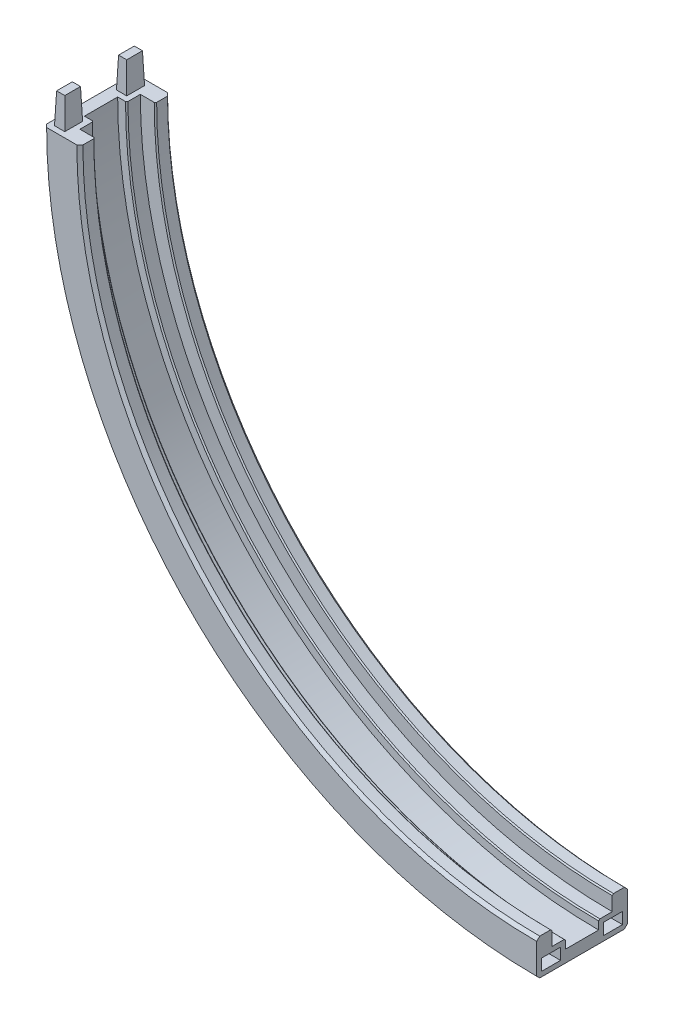
SolidWorks part; units mm, degrees
ref_plane "Plan de face" through (0, 0, 0) normal (0, 0, 1) x (1, 0, 0)
ref_plane "Plan de dessus" through (0, 0, 0) normal (0, 1, 0) x (1, 0, 0)
ref_plane "Plan de droite" through (0, 0, 0) normal (1, 0, 0) x (0, 0, -1)
sketch "Esquisse1" plane through (0, 0, 0) normal (0, 0, 1) x (1, 0, 0)
  line L0 (-159.1549, 159.1549) -> (0, 159.1549) construction
  line L1 (0, 159.1549) -> (0, 0) construction
  circle A0 centre (0, 159.1549) radius 159.1549 construction
  arc A1 (0, 0) -> (-159.1549, 159.1549) centre (0, 159.1549) cw
  dimension "D1" = 318.3099
  dimension "D2" = 90
sketch "Esquisse2" plane through (0, 0, 0) normal (1, 0, 0) x (0, 0, -1)
  line L0 (-5.5, 0) -> (5.5, 0)
  line L2 (-10, 8) -> (-15, 8)
  line L5 (-15, 8) -> (-15, -4)
  line L6 (-15, -4) -> (15, -4)
  line L7 (15, -4) -> (15, 8)
  line L10 (15, 8) -> (10, 8)
  line L18 (-10, 8) -> (-10, 3)
  line L19 (10, 8) -> (10, 3)
  line L20 (-10, 3) -> (-5.5, 3)
  line L21 (-5.5, 3) -> (-5.5, 0)
  line L22 (10, 3) -> (5.5, 3)
  line L23 (5.5, 3) -> (5.5, 0)
  point P4 (0, 0)
  point P17 (0, -4)
  dimension "D1" = 4
  dimension "D2" = 20
  dimension "D3" = 5
  dimension "D4" = 5
  dimension "D5" = 3
  dimension "D6" = 11
sweep "Balayage1" add profiles "Esquisse2" path "Esquisse1"
chamfer "Chanfrein1" distance 1 angle 45 4 edges at (-115.368, 43.787, -15) (-115.368, 43.787, 15) (-106.8827, 52.2723, -15) (-106.8827, 52.2723, 15)
chamfer "Chanfrein3" distance 0.4 angle 45 4 edges at (-110.4182, 48.7367, 5.5) (-106.8827, 52.2723, 10) (-106.8827, 52.2723, -10) (-110.4182, 48.7367, -5.5)
sketch "Esquisse5" plane through (0, 0, 0) normal (1, 0, 0) x (0, 0, -1)
  line L0 (-15, 7) -> (-15, -3) construction
  line L1 (-13.4, -2.4) -> (-7.1, -2.4)
  line L2 (-13.4, -2.4) -> (-13.4, 1.4)
  line L3 (-13.4, 1.4) -> (-7.1, 1.4)
  line L4 (-7.1, -2.4) -> (-7.1, 1.4)
  line L5 (-13.4, -2.4) -> (-7.1, 1.4) construction
  line L6 (-13.4, 1.4) -> (-7.1, -2.4) construction
  line L7 (-14, -4) -> (14, -4) construction
  line L8 (-5.9, 3) -> (-10, 3) construction
  line L9 (-5.5, 0) -> (-5.5, 2.6) construction
  line L10 (0, 89.7352) -> (0, -89.7352) construction
  line L11 (13.4, -2.4) -> (7.1, -2.4)
  line L12 (7.1, -2.4) -> (7.1, 1.4)
  line L13 (13.4, 1.4) -> (7.1, 1.4)
  line L14 (13.4, -2.4) -> (13.4, 1.4)
  point P0 (-10.25, -0.5)
  dimension "D1" = 1.6
  dimension "D2" = 1.6
  dimension "D3" = 1.6
  dimension "D4" = 1.6
extrude "Enlèv. mat.-Extru.1" cut sketch "Esquisse5" against normal blind 11 draft 2
sketch "Esquisse6" plane through (0, 159.1549, 0) normal (0, 1, 0) x (1, 0, 0)
  line L0 (-152.1549, -15) -> (-162.1549, -15) construction
  line L1 (-157.9549, -13.2) -> (-161.3549, -13.2)
  line L2 (-157.9549, -13.2) -> (-157.9549, -7.3)
  line L3 (-157.9549, -7.3) -> (-161.3549, -7.3)
  line L4 (-161.3549, -13.2) -> (-161.3549, -7.3)
  line L5 (-157.9549, -13.2) -> (-161.3549, -7.3) construction
  line L6 (-157.9549, -7.3) -> (-161.3549, -13.2) construction
  line L7 (-163.1549, -14) -> (-163.1549, 14) construction
  line L8 (-156.1549, -5.9) -> (-156.1549, -10) construction
  line L9 (-159.1549, -5.5) -> (-156.5549, -5.5) construction
  line L10 (-89.7352, 0) -> (89.7352, 0) construction
  line L11 (-157.9549, 13.2) -> (-157.9549, 7.3)
  line L12 (-157.9549, 7.3) -> (-161.3549, 7.3)
  line L13 (-161.3549, 13.2) -> (-161.3549, 7.3)
  line L14 (-157.9549, 13.2) -> (-161.3549, 13.2)
  point P0 (-159.6549, -10.25)
  dimension "D1" = 1.8
  dimension "D2" = 1.8
  dimension "D3" = 1.8
  dimension "D4" = 1.8
extrude "Boss.-Extru.2" add sketch "Esquisse6" along normal blind 10 draft 2
